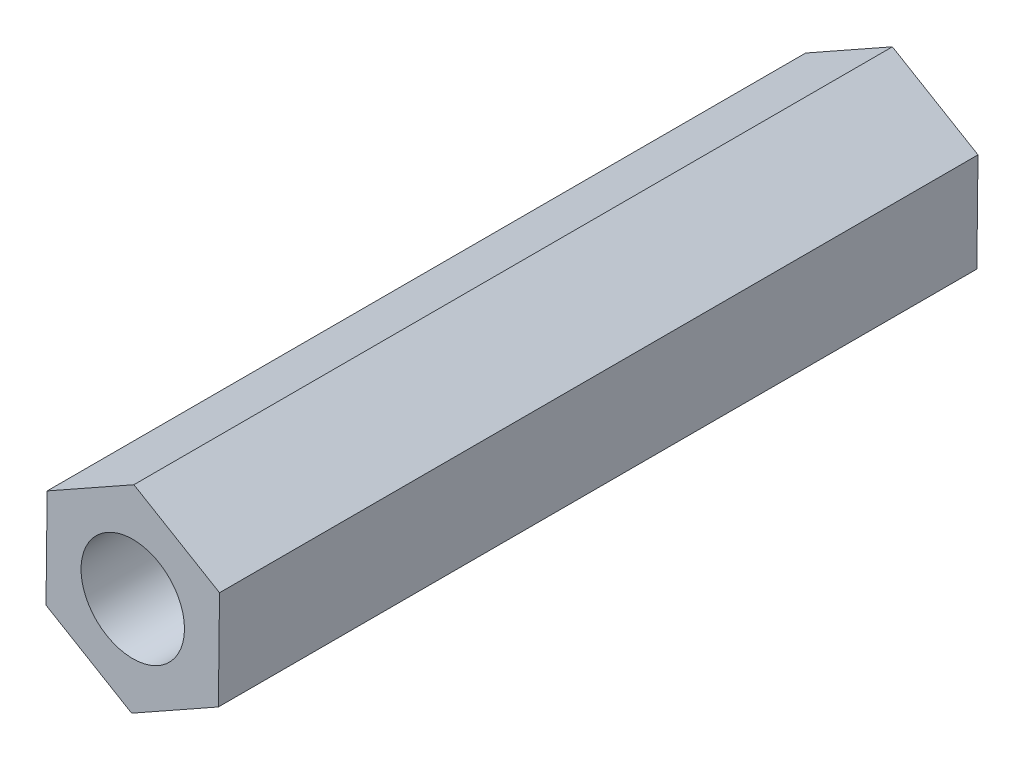
SolidWorks part; units mm, degrees
ref_plane "Ön Düzlem" through (0, 0, 0) normal (0, 0, 1) x (1, 0, 0)
ref_plane "Üst Düzlem" through (0, 0, 0) normal (0, 1, 0) x (1, 0, 0)
ref_plane "Sağ Düzlem" through (0, 0, 0) normal (1, 0, 0) x (0, 0, -1)
sketch "Çizim1" plane through (0, 0, 0) normal (0, 0, 1) x (1, 0, 0)
  line L1 (-2.4832, 1.4721) -> (-2.5165, -1.4144)
  line L2 (-2.5165, -1.4144) -> (-0.0333, -2.8866)
  line L3 (-0.0333, -2.8866) -> (2.4832, -1.4721)
  line L4 (2.4832, -1.4721) -> (2.5165, 1.4144)
  line L5 (2.5165, 1.4144) -> (0.0333, 2.8866)
  line L6 (0.0333, 2.8866) -> (-2.4832, 1.4721)
  circle A0 centre (0, 0) radius 2.5 construction
  circle A1 centre (0, 0) radius 1.5
  dimension "D1" = 5
  dimension "D2" = 3
extrude "Yükseklik-Ekstrüzyon1" add sketch "Çizim1" along normal blind 22
